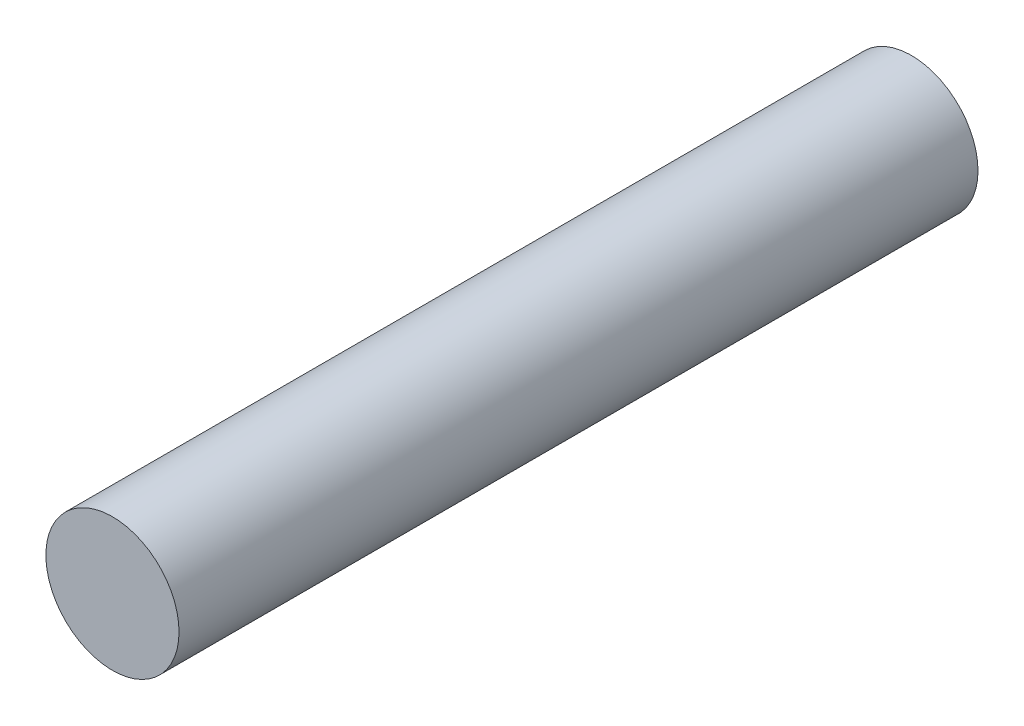
SolidWorks part; units mm, degrees
ref_plane "Front Plane" through (0, 0, 0) normal (0, 0, 1) x (1, 0, 0)
ref_plane "Top Plane" through (0, 0, 0) normal (0, 1, 0) x (1, 0, 0)
ref_plane "Right Plane" through (0, 0, 0) normal (1, 0, 0) x (0, 0, -1)
sketch "Sketch1" plane through (0, 0, 0) normal (0, 0, 1) x (1, 0, 0)
  circle A0 centre (0, 0) radius 2.5
  dimension "D1" = 5
extrude "Boss-Extrude1" add sketch "Sketch1" along normal blind 30
